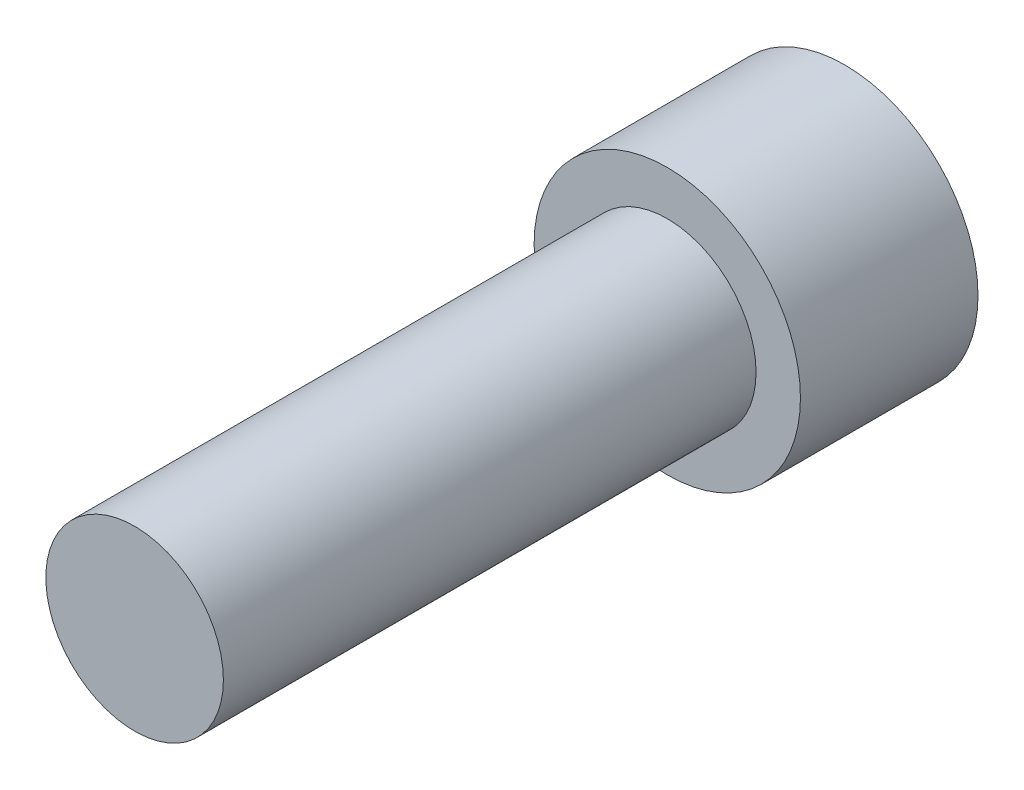
SolidWorks part; units mm, degrees
ref_plane "Alzado" through (0, 0, 0) normal (0, 0, 1) x (1, 0, 0)
ref_plane "Planta" through (0, 0, 0) normal (0, 1, 0) x (1, 0, 0)
ref_plane "Vista lateral" through (0, 0, 0) normal (1, 0, 0) x (0, 0, -1)
sketch "Croquis1" plane through (0, 0, 0) normal (0, 0, 1) x (1, 0, 0)
  circle A0 centre (0, 0) radius 0.75
  dimension "D1" = 1.5
extrude "Saliente-Extruir1" add sketch "Croquis1" along normal blind 1
ref_plane "Plano1" through (0, 0, 1) normal (0, 0, 1) x (1, 0, 0)
sketch "Croquis2" plane through (0, 0, 1) normal (0, 0, 1) x (1, 0, 0)
  circle A0 centre (0, 0) radius 0.5
  dimension "D1" = 1
extrude "Saliente-Extruir2" add sketch "Croquis2" along normal blind 3
ref_plane "Plano2" through (0, 0, 0) normal (0, 0, -1) x (-1, 0, 0)
sketch "Croquis3" plane through (0, 0, 0) normal (0, 0, -1) x (-1, 0, 0)
  line L1 (0.5774, 0) -> (0.2887, 0.5)
  line L2 (0.2887, 0.5) -> (-0.2887, 0.5)
  line L3 (-0.2887, 0.5) -> (-0.5774, 0)
  line L4 (-0.5774, 0) -> (-0.2887, -0.5)
  line L5 (-0.2887, -0.5) -> (0.2887, -0.5)
  line L6 (0.2887, -0.5) -> (0.5774, 0)
  circle A0 centre (0, 0) radius 0.5 construction
  dimension "D1" = 1
extrude "Cortar-Extruir1" cut sketch "Croquis3" against normal blind 0.75
